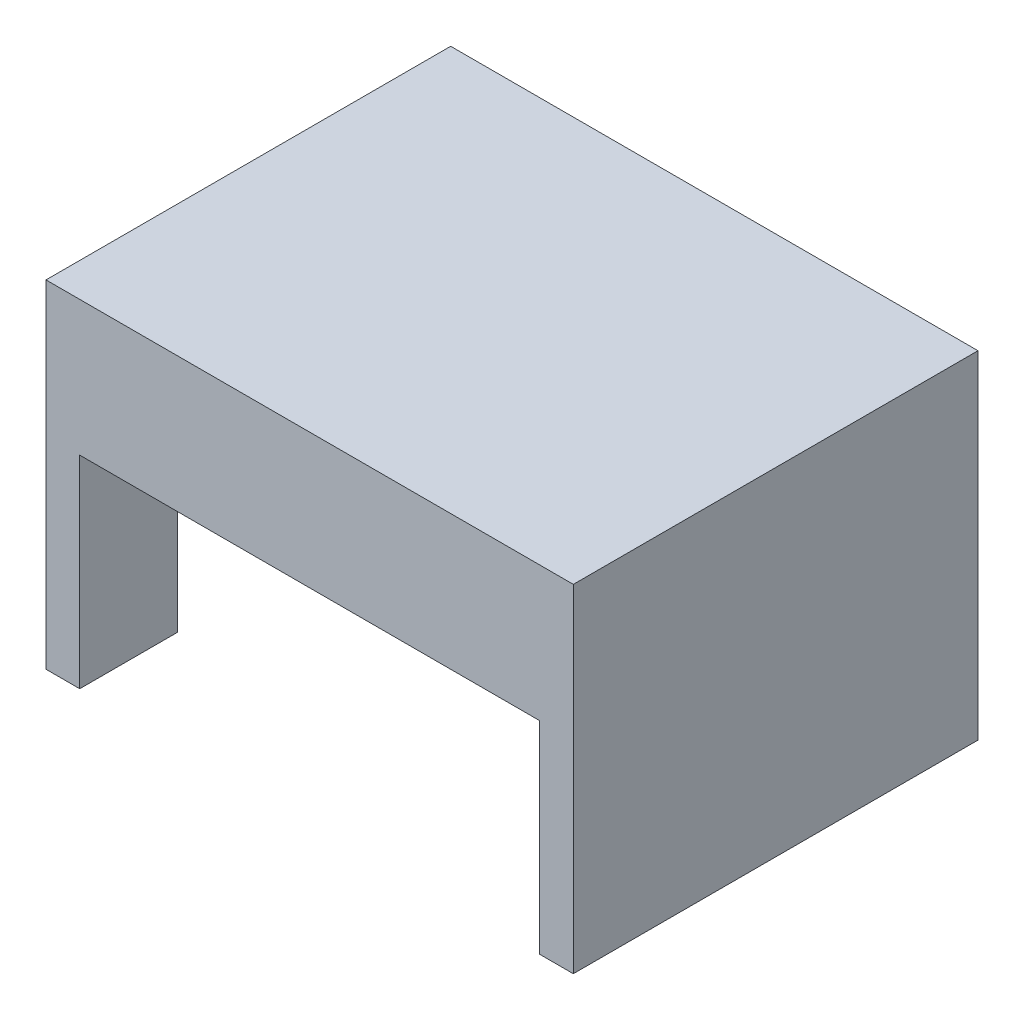
SolidWorks part; units mm, degrees
ref_plane "前基準面" through (0, 0, 0) normal (0, 0, 1) x (1, 0, 0)
ref_plane "上基準面" through (0, 0, 0) normal (0, 1, 0) x (1, 0, 0)
ref_plane "右基準面" through (0, 0, 0) normal (1, 0, 0) x (0, 0, -1)
sketch "草圖1" plane through (0, 0, 0) normal (0, 0, 1) x (1, 0, 0)
  line L1 (-56.4104, -6.4286) -> (-51.4104, -6.4286)
  line L2 (-56.4104, -6.4286) -> (-56.4104, -36.4286)
  line L3 (-56.4104, -36.4286) -> (-51.4104, -36.4286)
  line L4 (-51.4104, -6.4286) -> (-51.4104, -36.4286)
  line L5 (-56.4104, -6.4286) -> (21.7764, -6.4286)
  line L6 (-56.4104, -6.4286) -> (-56.4104, 13.5714)
  line L7 (-56.4104, 13.5714) -> (21.7764, 13.5714)
  line L8 (21.7764, -6.4286) -> (21.7764, 13.5714)
  line L9 (21.7764, -6.4286) -> (16.7764, -6.4286)
  line L10 (21.7764, -6.4286) -> (21.7764, -36.4286)
  line L11 (21.7764, -36.4286) -> (16.7764, -36.4286)
  line L12 (16.7764, -6.4286) -> (16.7764, -36.4286)
  dimension "D1" = 30
  dimension "D2" = 5
  dimension "D3" = 5
  dimension "D4" = 20
extrude "填料-伸長1" add sketch "草圖1" along normal blind 60 contours L5 L8 L7 L6 L1 | L5 L12 L11 L10
sketch "草圖2" plane through (0, -6.4286, 0) normal (0, -1, 0) x (1, 0, 0)
  line L0 (-51.4104, 60) -> (-51.4104, 0) construction
  line L1 (-51.4104, 14.5) -> (16.7764, 14.5)
  line L2 (-51.4104, 14.5) -> (-51.4104, 45.5)
  line L3 (-51.4104, 45.5) -> (16.7764, 45.5)
  line L4 (16.7764, 14.5) -> (16.7764, 45.5)
  line L5 (16.7764, 60) -> (16.7764, 0) construction
  line L6 (-51.4104, 60) -> (16.7764, 60) construction
  line L7 (-51.4104, 0) -> (16.7764, 0) construction
  dimension "D1" = 14.5
  dimension "D2" = 14.5
extrude "除料-伸長1" cut sketch "草圖2" against normal blind 10
sketch "草圖3" plane through (0, -36.4286, 0) normal (0, -1, 0) x (1, 0, 0)
  line L0 (-51.4104, 60) -> (-51.4104, 0) construction
  line L1 (-51.4104, 14.5) -> (-56.4104, 14.5)
  line L2 (-51.4104, 14.5) -> (-51.4104, 45.5)
  line L3 (-51.4104, 45.5) -> (-56.4104, 45.5)
  line L4 (-56.4104, 14.5) -> (-56.4104, 45.5)
  line L5 (-56.4104, 60) -> (-56.4104, 0) construction
  line L6 (-56.4104, 0) -> (-51.4104, 0) construction
  line L7 (-56.4104, 60) -> (-51.4104, 60) construction
  point P10 (-53.9104, 45.5)
  dimension "D1" = 14.5
  dimension "D2" = 14.5
extrude "除料-伸長3" cut sketch "草圖3" against normal blind 40
